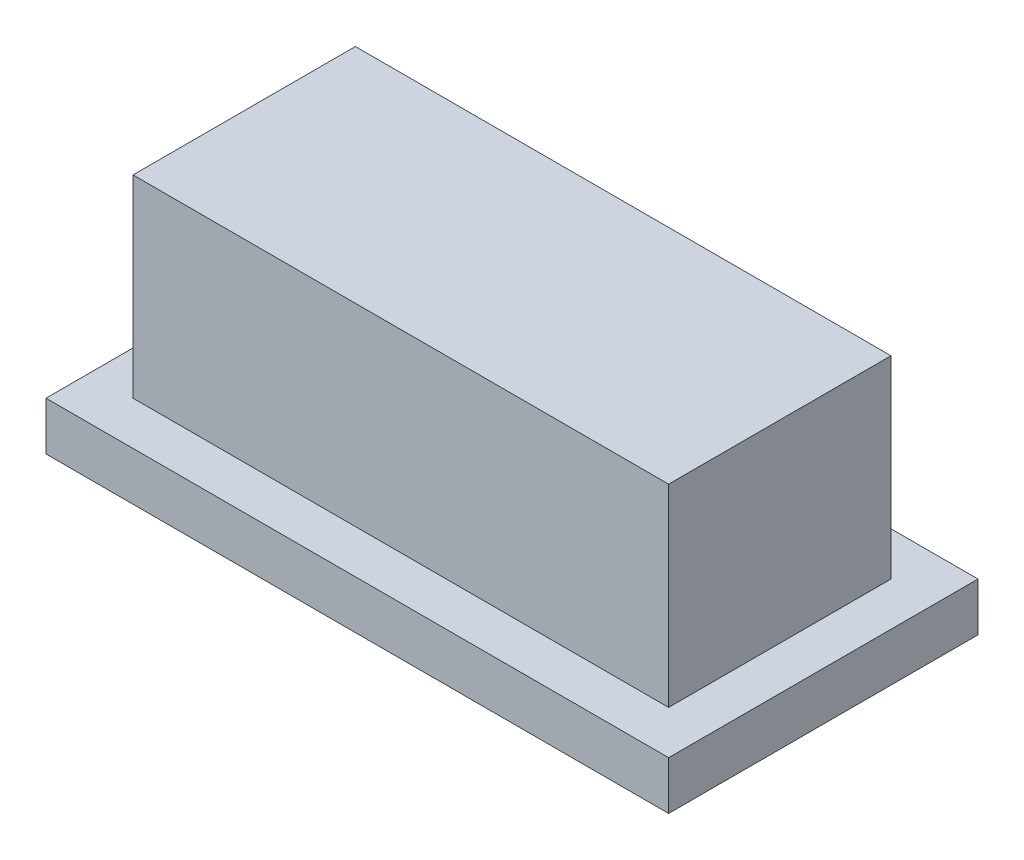
SolidWorks part; units mm, degrees
ref_plane "Front Plane" through (0, 0, 0) normal (0, 0, 1) x (1, 0, 0)
ref_plane "Top Plane" through (0, 0, 0) normal (0, 1, 0) x (1, 0, 0)
ref_plane "Right Plane" through (0, 0, 0) normal (1, 0, 0) x (0, 0, -1)
sketch "Sketch1" plane through (0, 0, 0) normal (0, 1, 0) x (1, 0, 0)
  line L0 (0, 6.4) -> (12.88, 6.4)
  line L5 (12.88, 0) -> (12.88, 6.4)
  line L6 (0, 0) -> (12.88, 0)
  line L7 (0, 0) -> (0, 6.4)
  dimension "D1" = 6.4
  dimension "D2" = 12.88
extrude "Boss-Extrude1" add sketch "Sketch1" along normal blind 1
sketch "Sketch3" plane through (0, 1, 0) normal (0, 1, 0) x (1, 0, 0)
  line L8 (0.9, 5.5) -> (0.9, 0.9)
  line L9 (0.9, 0.9) -> (11.98, 0.9)
  line L10 (11.98, 0.9) -> (11.98, 5.5)
  line L11 (11.98, 5.5) -> (0.9, 5.5)
  line L12 (0.9, 5.5) -> (0.9, 0.9)
  line L13 (0.9, 0.9) -> (11.98, 0.9)
  line L14 (11.98, 0.9) -> (11.98, 5.5)
  line L15 (11.98, 5.5) -> (0.9, 5.5)
  dimension "D1" = 0.9
extrude "Boss-Extrude2" add sketch "Sketch3" along normal blind 4
sketch "Sketch4" plane through (0, 0, 0) normal (0, -1, 0) x (1, 0, 0)
  line L0 (0, 0) -> (0, -6.4) construction
  line L1 (4.84, -2.1) -> (8.04, -2.1)
  line L2 (4.84, -2.1) -> (4.84, -4.3)
  line L3 (4.84, -4.3) -> (8.04, -4.3)
  line L4 (8.04, -2.1) -> (8.04, -4.3)
  line L5 (0, 0) -> (12.88, 0) construction
  dimension "D1" = 3.2
  dimension "D2" = 2.2
  dimension "D3" = 4.84
  dimension "D4" = 2.1
extrude "Cut-Extrude1" cut sketch "Sketch4" against normal blind 3.1
